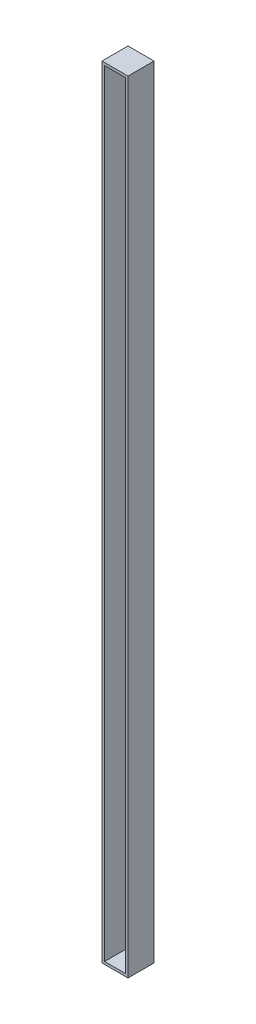
SolidWorks part; units mm, degrees
material "AISI 1020"
ref_plane "Front Plane" through (0, 0, 0) normal (0, 0, 1) x (1, 0, 0)
ref_plane "Top Plane" through (0, 0, 0) normal (0, 1, 0) x (1, 0, 0)
ref_plane "Right Plane" through (0, 0, 0) normal (1, 0, 0) x (0, 0, -1)
sketch "Sketch1" plane through (0, 0, 0) normal (0, 0, 1) x (1, 0, 0)
  line L1 (-31.7391, 49.7826) -> (-11.7391, 49.7826)
  line L2 (-31.7391, 49.7826) -> (-31.7391, -550.2174)
  line L3 (-31.7391, -550.2174) -> (-11.7391, -550.2174)
  line L4 (-11.7391, 49.7826) -> (-11.7391, -550.2174)
  dimension "D1" = 20
  dimension "D2" = 600
extrude "Boss-Extrude1" add sketch "Sketch1" against normal blind 20
sketch "Sketch2" plane through (0, 0, 0) normal (0, 0, 1) x (1, 0, 0)
  line L8 (-29.7391, 47.7826) -> (-29.7391, -548.2174)
  line L9 (-29.7391, -548.2174) -> (-13.7391, -548.2174)
  line L10 (-13.7391, -548.2174) -> (-13.7391, 47.7826)
  line L11 (-13.7391, 47.7826) -> (-29.7391, 47.7826)
  line L12 (-29.7391, 47.7826) -> (-29.7391, -548.2174)
  line L13 (-29.7391, -548.2174) -> (-13.7391, -548.2174)
  line L14 (-13.7391, -548.2174) -> (-13.7391, 47.7826)
  line L15 (-13.7391, 47.7826) -> (-29.7391, 47.7826)
  dimension "D1" = 2
extrude "Cut-Extrude1" cut sketch "Sketch2" against normal blind 18 contours L12 L13 L14 L15
